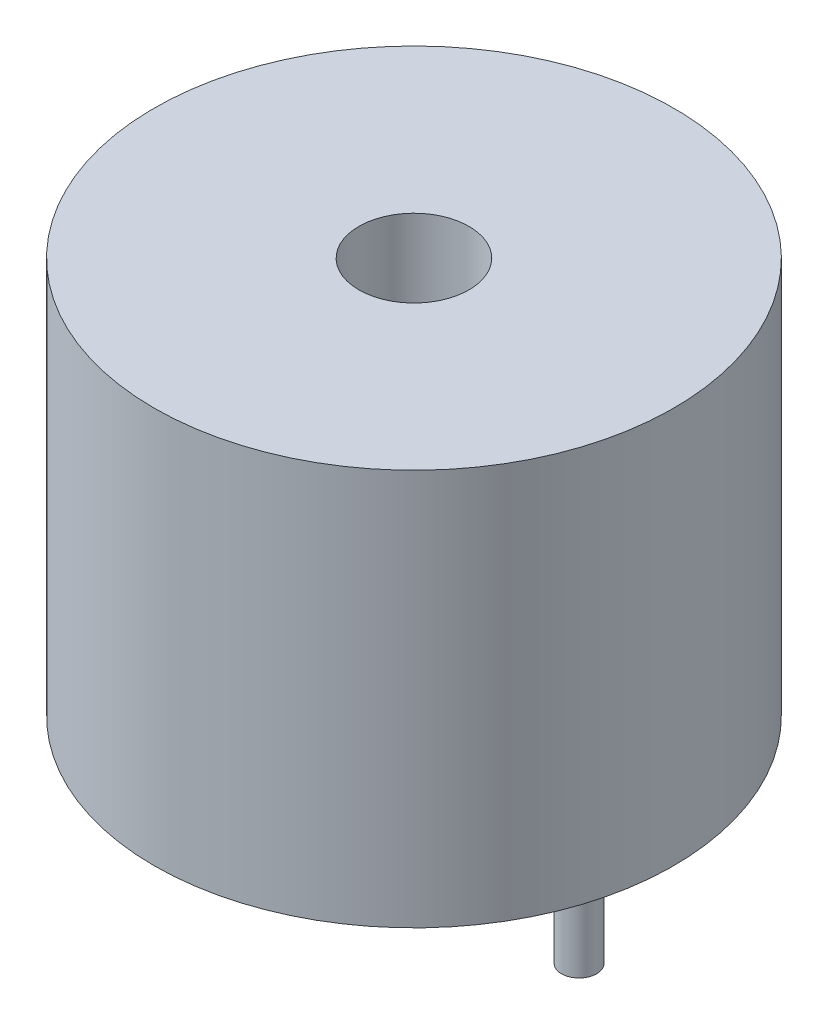
SolidWorks part; units mm, degrees
ref_plane "Plan de face" through (0, 0, 0) normal (0, 0, 1) x (1, 0, 0)
ref_plane "Plan de dessus" through (0, 0, 0) normal (0, 1, 0) x (1, 0, 0)
ref_plane "Plan de droite" through (0, 0, 0) normal (1, 0, 0) x (0, 0, -1)
sketch "Esquisse1" plane through (0, 0, 0) normal (0, 1, 0) x (1, 0, 0)
  circle A0 centre (0, 0) radius 5.9
  dimension "D1" = 11.8
extrude "Boss.-Extru.1" add sketch "Esquisse1" along normal blind 9
sketch "Esquisse2" plane through (0, 9, 0) normal (0, 1, 0) x (1, 0, 0)
  circle A0 centre (0, 0) radius 1.25
  dimension "D1" = 2.5
extrude "Enlèv. mat.-Extru.1" cut sketch "Esquisse2" against normal blind 3
sketch "Esquisse3" plane through (0, 0, 0) normal (0, -1, 0) x (1, 0, 0)
  line L0 (-3.75, 0) -> (3.75, 0) construction
  circle A0 centre (3.75, 0) radius 0.4
  circle A1 centre (-3.75, 0) radius 0.4
  point P4 (1.3377, -0.482)
  point P5 (0, 0)
  dimension "D2" = 0.8
  dimension "D3" = 0.8
  dimension "D1" = 7.5
extrude "Boss.-Extru.2" add sketch "Esquisse3" along normal blind 3
ref_plane "Plan1" through (0, 0, 0.4) normal (0, 0, 1) x (1, 0, 0)
